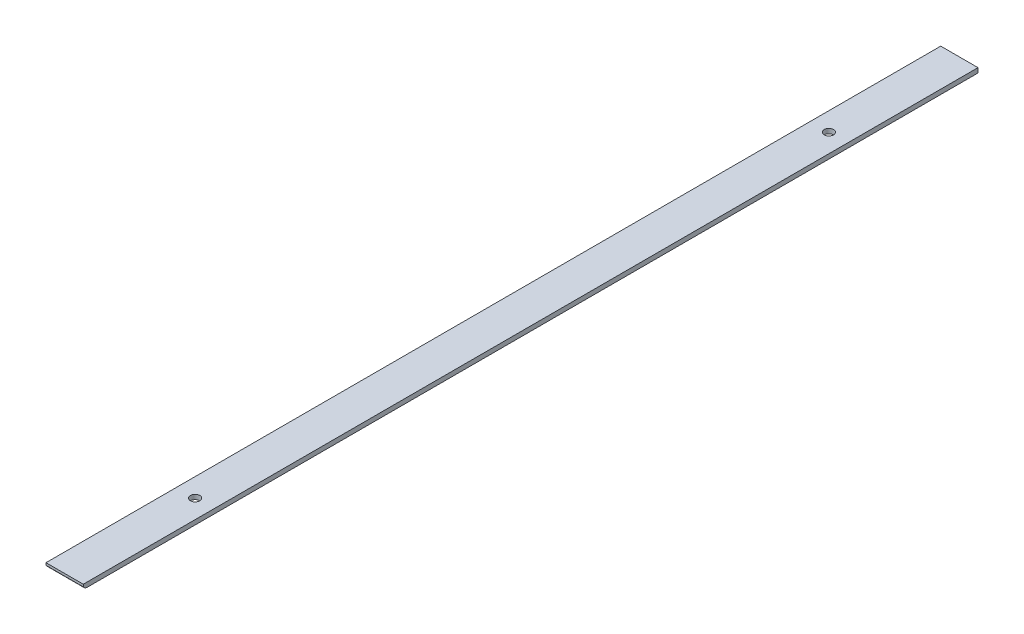
SolidWorks part; units mm, degrees
material "1023 Carbon Steel Sheet (SS)"
ref_plane "Front" through (0, 0, 0) normal (0, 0, 1) x (1, 0, 0)
ref_plane "Top" through (0, 0, 0) normal (0, 1, 0) x (1, 0, 0)
ref_plane "Right" through (0, 0, 0) normal (1, 0, 0) x (0, 0, -1)
sketch "Sketch1" plane through (0, 0, 0) normal (1, 0, 0) x (0, 0, -1)
  line L0 (-23.5845, 0) -> (-23.5845, -1.5875)
  line L1 (-23.5845, 0) -> (586.0155, 0)
  line L3 (-20.8349, -3.175) -> (586.0155, -3.175)
  line L4 (586.0155, 0) -> (586.0155, -3.175)
  line L5 (-23.5845, 78.2056) -> (-23.5845, 75.0192) construction
  arc A0 (-23.5845, -1.5875) -> (-20.8349, -3.175) centre (-20.8349, 0) ccw
  point P2 (0, 0)
  point P8 (0, -3.175)
  point P11 (0, 0)
  dimension "D1" = 3.175
  dimension "D2" = 1.5875
  dimension "D3" = 609.6
extrude "Boss-Extrude1" add sketch "Sketch1" along normal blind 25.4
sketch "Sketch2" plane through (0, 0, 0) normal (0, 1, 0) x (1, 0, 0)
  line L0 (12.7, 0) -> (12.7, 19.1815) construction
  line L2 (25.4, -23.5845) -> (0, -23.5845) construction
  line L3 (25.4, 586.0155) -> (0, 586.0155) construction
  circle A0 centre (12.7, 65.3155) radius 3.175
  circle A1 centre (12.7, 497.1155) radius 3.175
  point P3 (12.7, -23.5845)
  dimension "D1" = 6.35
  dimension "D2" = 88.9
  dimension "D3" = 88.9
extrude "Cut-Extrude1" cut sketch "Sketch2" against normal through all
sketch "Sketch3" plane through (0, -3.175, 0) normal (0, -1, 0) x (1, 0, 0)
  circle A0 centre (12.7, -65.3155) radius 4.7625
  circle A1 centre (12.7, -497.1155) radius 4.7625
  dimension "D1" = 9.525
equation "\"12ion\"=3.48165"
